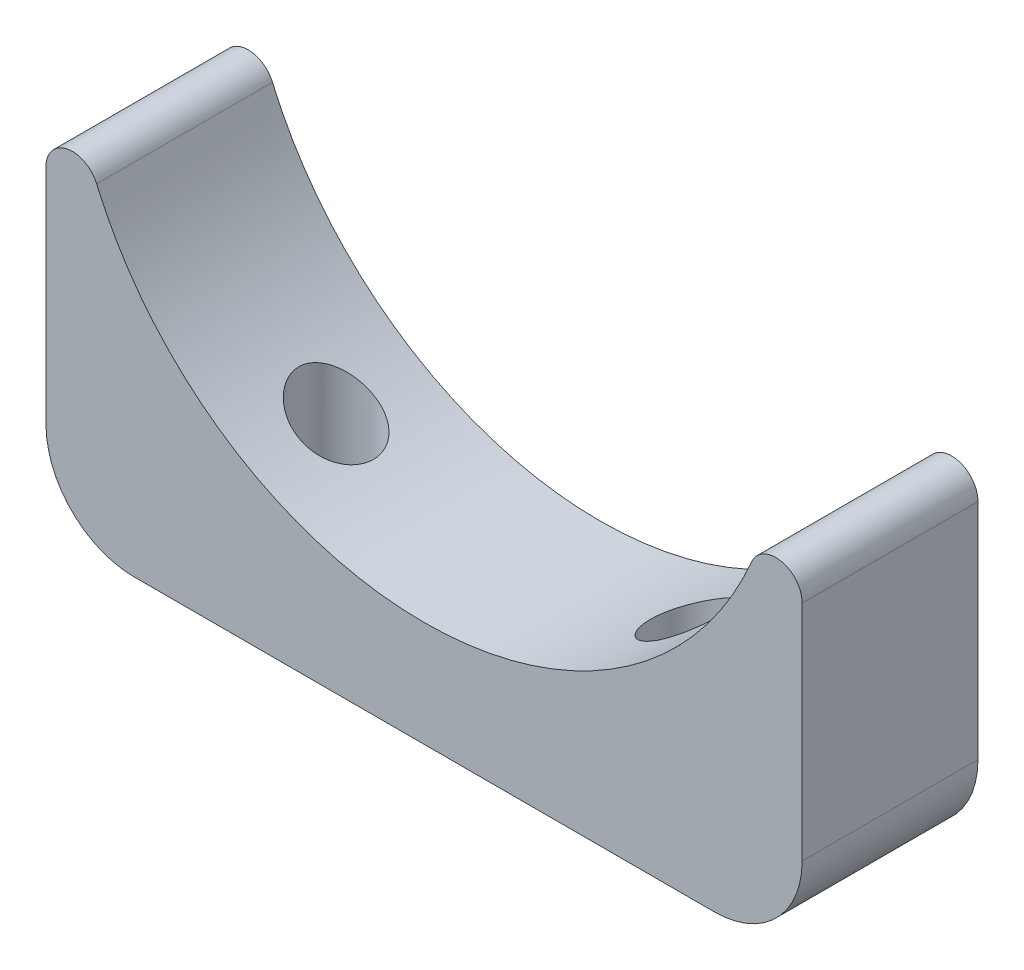
SolidWorks part; units mm, degrees
ref_plane "Plane1" through (0, 0, 0) normal (0, 0, 1) x (1, 0, 0)
ref_plane "Plane2" through (0, 0, 0) normal (0, 1, 0) x (1, 0, 0)
ref_plane "Plane3" through (0, 0, 0) normal (1, 0, 0) x (0, 0, -1)
sketch "Sketch1" plane through (0, 0, 0) normal (0, 0, 1) x (1, 0, 0)
  line L0 (0, 0) -> (0, -52.5) construction
  line L1 (43, -17.0953) -> (43, -42.5)
  line L2 (33, -52.5) -> (-33, -52.5)
  line L3 (-43, -17.0953) -> (-43, -42.5)
  arc A0 (-37.2414, -15.9163) -> (37.2414, -15.9163) centre (0, 0) ccw
  arc A1 (37.2414, -15.9163) -> (43, -17.0953) centre (40, -17.0953) cw
  arc A2 (-37.2414, -15.9163) -> (-43, -17.0953) centre (-40, -17.0953) ccw
  arc A3 (43, -42.5) -> (33, -52.5) centre (33, -42.5) cw
  arc A4 (-43, -42.5) -> (-33, -52.5) centre (-33, -42.5) ccw
  point P13 (43, -52.5)
  point P16 (-43, -52.5)
  dimension "D1" = 3
  dimension "D2" = 40.5
  dimension "D5" = 10
  dimension "D3" = 52.5
  dimension "D4" = 86
extrude "Base-Extrude" add sketch "Sketch1" along normal mid plane 20
hole_wizard "Hole1" positions "Sketch3" profile "Sketch2" legacy
sketch "Sketch3" plane through (0, -52.5, 0) normal (0, -1, 0) x (1, 0, 0)
  line L0 (0, 0) -> (0, 10) construction
  line L1 (0, 10) -> (0, -10) construction
  point P0 (-20, 0)
  point P6 (20, 0)
  dimension "D1" = 40
sketch "Sketch2" plane through (-20, -52.5, 0) normal (1, 0, 0) x (0, 0, -1)
  line L0 (0, 0) -> (0, 32.5537)
  line L1 (0, 32.5537) -> (4.25, 30)
  line L2 (4.25, 30) -> (4.25, 0)
  line L4 (4.25, 0) -> (0, 0)
  line L6 (0, 32.5537) -> (-4.25, 30) construction
  line L7 (0, -4.2442) -> (0, 117.3081) construction
  dimension "Diameter" = 8.5
  dimension "Depth" = 30
  dimension "Drill Angle" = 118
cosmetic thread "Cosmetic Thread1" parameters "D2"=10
cosmetic thread "Cosmetic Thread2" parameters "D2"=10
